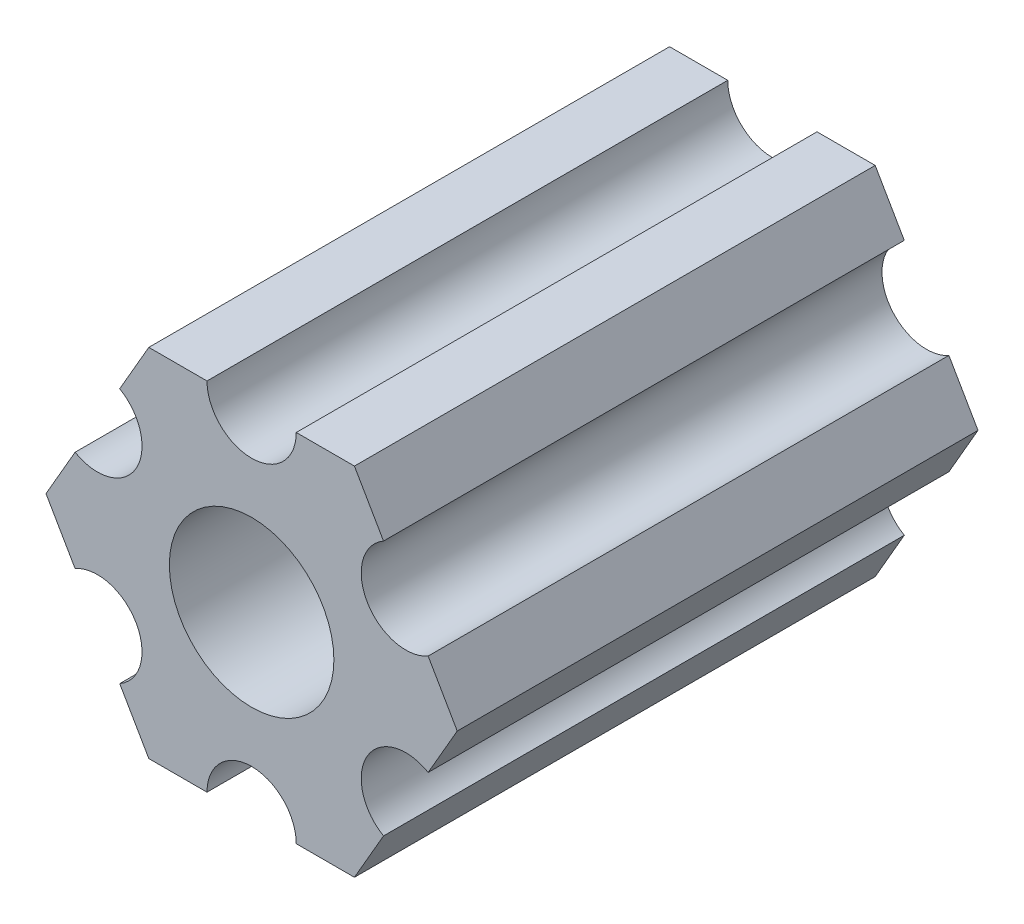
SolidWorks part; units mm, degrees
ref_plane "Front Plane" through (0, 0, 0) normal (0, 0, 1) x (1, 0, 0)
ref_plane "Top Plane" through (0, 0, 0) normal (0, 1, 0) x (1, 0, 0)
ref_plane "Right Plane" through (0, 0, 0) normal (1, 0, 0) x (0, 0, -1)
ref_plane "Plane1" through (0, 0, 0) normal (0, 0, -1) x (-1, 0, 0)
sketch "Sketch1" plane through (0, 0, 0) normal (0, 0, -1) x (-1, 0, 0)
  line L0 (-4.7036, -4.5531) -> (-3.6662, -6.35)
  line L1 (-3.6662, -6.35) -> (-1.5913, -6.35)
  line L2 (1.5913, -6.35) -> (3.6662, -6.35)
  line L3 (3.6662, -6.35) -> (4.7036, -4.5531)
  line L4 (6.2949, -1.7969) -> (7.3323, 0)
  line L5 (7.3323, 0) -> (6.2949, 1.7969)
  line L6 (4.7036, 4.5531) -> (3.6662, 6.35)
  line L7 (3.6662, 6.35) -> (1.5913, 6.35)
  line L8 (-1.5913, 6.35) -> (-3.6662, 6.35)
  line L9 (-3.6662, 6.35) -> (-4.7036, 4.5531)
  line L10 (-6.2949, 1.7969) -> (-7.3323, 0)
  line L11 (-7.3323, 0) -> (-6.2949, -1.7969)
  circle A0 centre (0, 0) radius 2.9337
  arc A1 (-6.2949, -1.7969) -> (-4.7036, -4.5531) centre (-5.4993, -3.175) cw
  arc A2 (-1.5913, -6.35) -> (1.5913, -6.35) centre (0, -6.35) cw
  arc A3 (4.7036, -4.5531) -> (6.2949, -1.7969) centre (5.4993, -3.175) cw
  arc A4 (6.2949, 1.7969) -> (4.7036, 4.5531) centre (5.4993, 3.175) cw
  arc A5 (1.5913, 6.35) -> (-1.5913, 6.35) centre (0, 6.35) cw
  arc A6 (-4.7036, 4.5531) -> (-6.2949, 1.7969) centre (-5.4993, 3.175) cw
extrude "Boss-Extrude1" add sketch "Sketch1" against normal blind 18.5699
